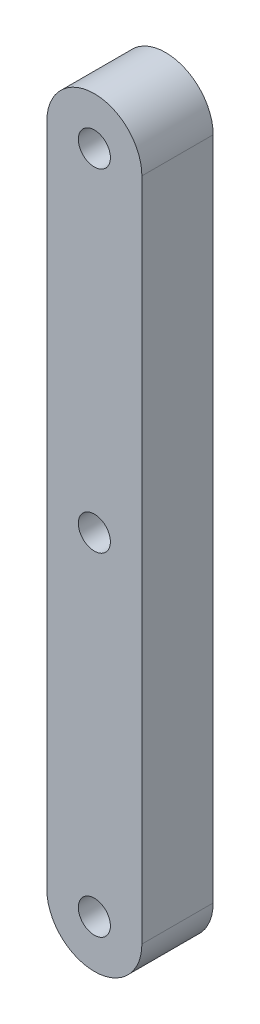
SolidWorks part; units mm, degrees
ref_plane "Front Plane" through (0, 0, 0) normal (0, 0, 1) x (1, 0, 0)
ref_plane "Top Plane" through (0, 0, 0) normal (0, 1, 0) x (1, 0, 0)
ref_plane "Right Plane" through (0, 0, 0) normal (1, 0, 0) x (0, 0, -1)
sketch "Sketch1" plane through (0, 0, 0) normal (0, 0, 1) x (1, 0, 0)
  line L0 (0, 0) -> (0, 71.12)
  line L1 (10.16, 71.12) -> (10.16, 0)
  arc A0 (0, 71.12) -> (10.16, 71.12) centre (5.08, 71.12) cw
  arc A1 (10.16, 0) -> (0, 0) centre (5.08, 0) cw
  circle A2 centre (5.08, 71.12) radius 1.7145
  circle A3 centre (5.08, 0) radius 1.7145
  dimension "D2" = 5.08
  dimension "D3" = 3.429
  dimension "D1" = 71.12
extrude "Boss-Extrude1" add sketch "Sketch1" along normal blind 7.62
sketch "Sketch2" plane through (0, 0, 7.62) normal (0, 0, 1) x (1, 0, 0)
  line L1 (0, 71.12) -> (0, 0) construction
  circle A0 centre (5.08, 35.56) radius 1.7145
  arc A2 (0, 0) -> (10.16, 0) centre (5.08, 0) ccw construction
  point P7 (0, 35.56)
  point P11 (5.08, -5.08)
  dimension "D1" = 3.429
extrude "Cut-Extrude1" cut sketch "Sketch2" against normal blind 10.16
